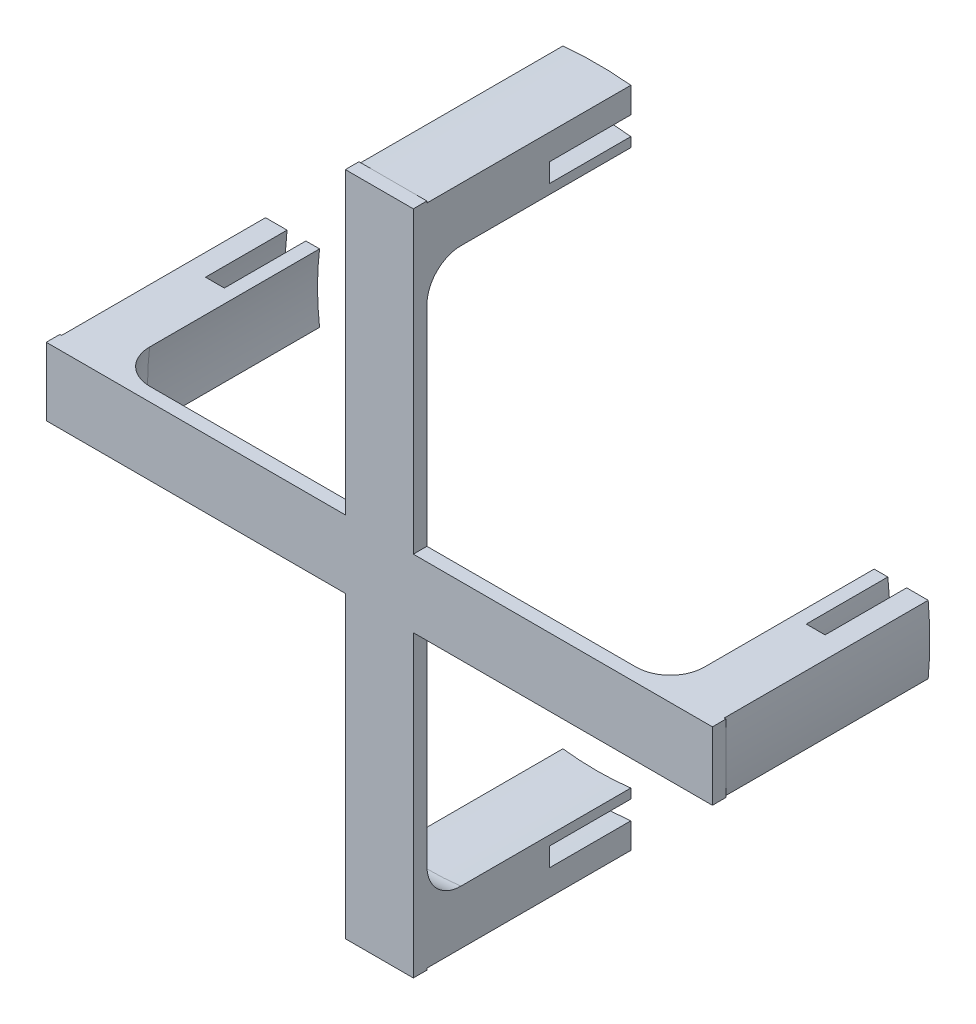
SolidWorks part; units mm, degrees
ref_plane "Front Plane" through (0, 0, 0) normal (0, 0, 1) x (1, 0, 0)
ref_plane "Top Plane" through (0, 0, 0) normal (0, 1, 0) x (1, 0, 0)
ref_plane "Right Plane" through (0, 0, 0) normal (1, 0, 0) x (0, 0, -1)
sketch "Sketch1" plane through (0, 0, 0) normal (0, 0, 1) x (1, 0, 0)
  line L1 (-5, 49) -> (5, 49)
  line L2 (-5, 49) -> (-5, -49)
  line L3 (-5, -49) -> (5, -49)
  line L4 (5, 49) -> (5, -49)
  line L5 (-5, 49) -> (5, -49) construction
  line L6 (-5, -49) -> (5, 49) construction
  line L7 (-49, 5) -> (49, 5)
  line L8 (-49, 5) -> (-49, -5)
  line L9 (-49, -5) -> (49, -5)
  line L10 (49, 5) -> (49, -5)
  line L11 (-49, 5) -> (49, -5) construction
  line L12 (-49, -5) -> (49, 5) construction
  point P0 (0, 0)
  point P6 (0, 0)
  dimension "D1" = 10
  dimension "D2" = 98
  dimension "D3" = 98
  dimension "D4" = 10
extrude "Boss-Extrude1" add sketch "Sketch1" along normal blind 2 contours L2 L9 L4 L7 | L8 L9 L2 L7 | L2 L7 L4 L1 | L10 L7 L4 L9 | L9 L2 L3 L4
sketch "Sketch3" plane through (0, 0, 0) normal (0, 0, -1) x (-1, 0, 0)
  line L0 (-48.7442, 5) -> (-40.7947, 5)
  line L1 (-5, 5) -> (-49, 5) construction
  line L2 (-48.7442, -5) -> (-40.7947, -5)
  line L3 (-5, -5) -> (-49, -5) construction
  line L4 (0, 0) -> (0, -20.0268) construction
  line L5 (0, -20.0268) -> (0, 0) construction
  line L6 (0, 0) -> (13.2459, 0) construction
  line L7 (5, 48.7442) -> (5, 40.7947)
  line L8 (-5, 48.7442) -> (-5, 40.7947)
  line L9 (48.7442, -5) -> (40.7947, -5)
  line L10 (48.7442, 5) -> (40.7947, 5)
  line L11 (-5, -48.7442) -> (-5, -40.7947)
  line L12 (5, -48.7442) -> (5, -40.7947)
  circle A0 centre (0, 0) radius 41.1 construction
  circle A1 centre (0, 0) radius 49 construction
  arc A2 (-48.7442, 5) -> (-48.7442, -5) centre (0, 0) ccw
  arc A3 (-40.7947, -5) -> (-40.7947, 5) centre (0, 0) cw
  arc A4 (-5, 40.7947) -> (5, 40.7947) centre (0, 0) cw
  arc A5 (5, 48.7442) -> (-5, 48.7442) centre (0, 0) ccw
  arc A6 (40.7947, 5) -> (40.7947, -5) centre (0, 0) cw
  arc A7 (48.7442, -5) -> (48.7442, 5) centre (0, 0) ccw
  arc A8 (5, -40.7947) -> (-5, -40.7947) centre (0, 0) cw
  arc A9 (-5, -48.7442) -> (5, -48.7442) centre (0, 0) ccw
  point P31 (0, 0)
  dimension "D1" = 98
  dimension "D2" = 82.2
  dimension "D3" = 4
extrude "Boss-Extrude2" add sketch "Sketch3" along normal blind 30
sketch "Sketch4" plane through (0, 0, -30) normal (0, 0, -1) x (-1, 0, 0)
  line L0 (-11.1056, -44.4847) -> (-11.4617, -41.548)
  line L1 (-48.7442, 5) -> (48.7442, 5) construction
  line L2 (-48.7442, 5) -> (-48.7442, -5) construction
  line L3 (-48.7442, -5) -> (48.7442, -5) construction
  line L4 (48.7442, 5) -> (48.7442, -5) construction
  line L5 (-48.7442, 5) -> (48.7442, -5) construction
  line L6 (-48.7442, -5) -> (48.7442, 5) construction
  line L7 (12.0012, -44.2515) -> (13.2547, -41.0113)
  line L8 (-14.1296, 43.6185) -> (-12.4442, 41.2644)
  line L9 (17.3222, 42.4519) -> (11.9297, 41.4161)
  arc A0 (-14.1296, 43.6185) -> (-11.1056, -44.4847) centre (0, 0) ccw
  arc A1 (-12.4442, 41.2644) -> (-11.4617, -41.548) centre (0, 0) ccw
  arc A2 (12.0012, -44.2515) -> (17.3222, 42.4519) centre (0, 0) ccw
  arc A3 (13.2547, -41.0113) -> (11.9297, 41.4161) centre (0, 0) ccw
  point P4 (0, 0)
  dimension "D1" = 91.7
  dimension "D2" = 86.2
extrude "Cut-Extrude1" cut sketch "Sketch4" against normal blind 12
sketch "Sketch5" plane through (0, 0, -30) normal (0, 0, -1) x (-1, 0, 0)
  line L0 (-42.0284, 16.7682) -> (-39.8163, 14.8631)
  line L1 (5, -48.7442) -> (-5, -48.7442) construction
  line L2 (5, -48.7442) -> (5, 48.7442) construction
  line L3 (5, 48.7442) -> (-5, 48.7442) construction
  line L4 (-5, -48.7442) -> (-5, 48.7442) construction
  line L5 (5, -48.7442) -> (-5, 48.7442) construction
  line L6 (5, 48.7442) -> (-5, -48.7442) construction
  line L7 (-42.2682, -16.1543) -> (-39.6994, -15.1725)
  line L8 (42.1092, 16.5644) -> (39.1391, 16.5644)
  line L9 (40.0078, -21.141) -> (38.619, -17.7432)
  arc A0 (39.1391, 16.5644) -> (-39.8163, 14.8631) centre (0, 0) ccw
  arc A1 (42.1092, 16.5644) -> (-42.0284, 16.7682) centre (0, 0) ccw
  arc A2 (-42.2682, -16.1543) -> (40.0078, -21.141) centre (0, 0) ccw
  arc A3 (-39.6994, -15.1725) -> (38.619, -17.7432) centre (0, 0) ccw
  point P4 (0, 0)
  dimension "D1" = 85
  dimension "D2" = 90.5
extrude "Cut-Extrude2" cut sketch "Sketch5" against normal blind 12
fillet "Fillet1" radius 5 4 edges at (0, -41.1, 0) (0, 41.1, 0) (-41.1, 0, 0) (41.1, 0, 0)
